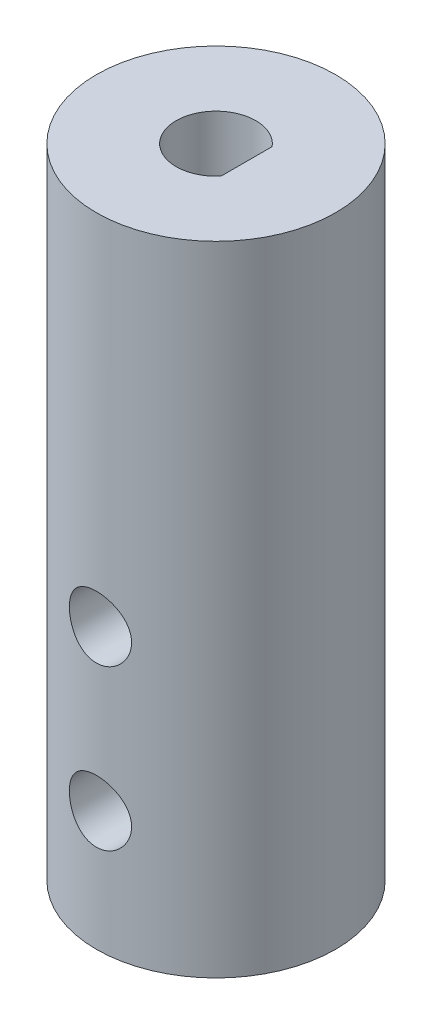
SolidWorks part; units mm, degrees
ref_plane "Front Plane" through (0, 0, 0) normal (0, 0, 1) x (1, 0, 0)
ref_plane "Top Plane" through (0, 0, 0) normal (0, 1, 0) x (1, 0, 0)
ref_plane "Right Plane" through (0, 0, 0) normal (1, 0, 0) x (0, 0, -1)
sketch "Sketch1" plane through (0, 0, 0) normal (0, 1, 0) x (1, 0, 0)
  line L0 (2.4396, -2.032) -> (2.4396, 2.032)
  circle A0 centre (0, 0) radius 9.525
  circle A1 centre (0, 0) radius 3.175
  dimension "D1" = 19.05
  dimension "D2" = 6.35
  dimension "D3" = 4.064
extrude "Boss-Extrude1" add sketch "Sketch1" along normal blind 50.8 contours L0 A1 | A0 A1
ref_plane "Plane1" through (0, 0, 9.525) normal (0, 0, 1) x (1, 0, 0)
sketch "Sketch2" plane through (0, 0, 9.525) normal (0, 0, 1) x (1, 0, 0)
  line L0 (-9.525, 50.8) -> (-9.525, 0) construction
  line L1 (-9.525, 0) -> (9.525, 0) construction
  line L2 (-9.525, 50.8) -> (-9.525, 0) construction
  circle A0 centre (0, 9.525) radius 2.4765
  circle A1 centre (0, 22.225) radius 2.4765
  dimension "D1" = 4.953
  dimension "D4" = 4.953
  dimension "D2" = 9.525
  dimension "D3" = 9.525
  dimension "D5" = 12.7
  dimension "D6" = 9.525
extrude "Cut-Extrude1" cut sketch "Sketch2" against normal through all
